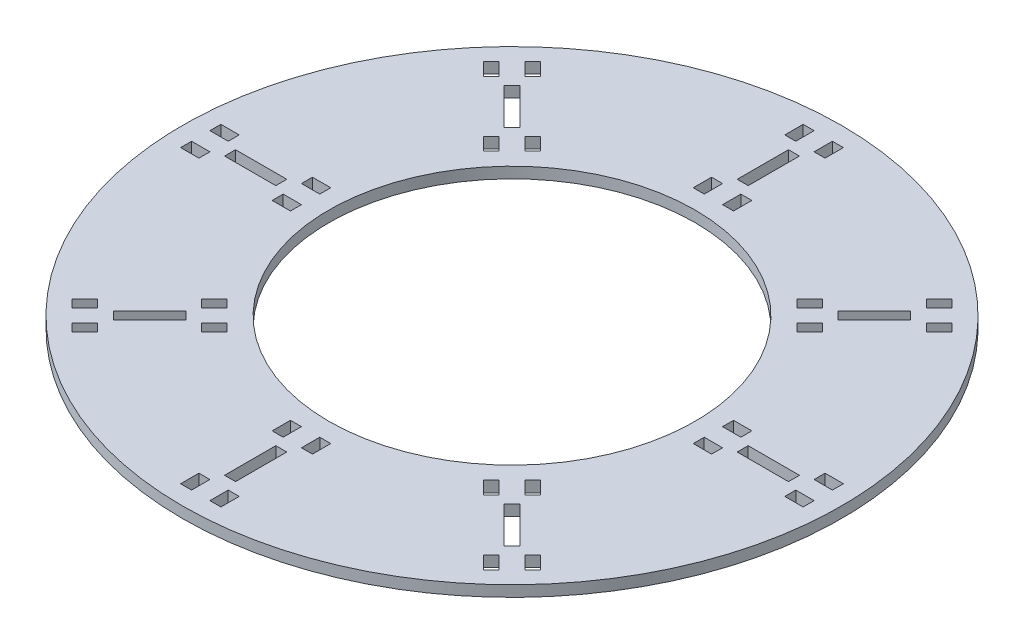
SolidWorks part; units mm, degrees
ref_plane "Front Plane" through (0, 0, 0) normal (0, 0, 1) x (1, 0, 0)
ref_plane "Top Plane" through (0, 0, 0) normal (0, 1, 0) x (1, 0, 0)
ref_plane "Right Plane" through (0, 0, 0) normal (1, 0, 0) x (0, 0, -1)
sketch "Sketch1" plane through (0, 0, 0) normal (0, 1, 0) x (1, 0, 0)
  circle A0 centre (0, 0) radius 90
  dimension "D1" = 180
extrude "Boss-Extrude1" add sketch "Sketch1" along normal blind 3
sketch "Sketch2" plane through (0, 3, 0) normal (0, 1, 0) x (1, 0, 0)
  line L1 (-1.5, 77) -> (1.5, 77)
  line L2 (-1.5, 77) -> (-1.5, 63)
  line L3 (-1.5, 63) -> (1.5, 63)
  line L4 (1.5, 77) -> (1.5, 63)
  point P4 (0, 63)
  point P6 (-1.5, 70)
  dimension "D1" = 3
  dimension "D2" = 14
  dimension "D3" = 70
extrude "Cut-Extrude2" cut sketch "Sketch2" against normal blind 3
sketch "Sketch15" plane through (0, 3, 0) normal (0, 1, 0) x (1, 0, 0)
  line L0 (0, 0) -> (0, 45.806) construction
pattern_circular "CirPattern1" count 8 over 360 about axis through (0, 0, 0) along (0, 1, 0) of "Cut-Extrude2"
sketch "Sketch16" plane through (0, 3, 0) normal (0, 1, 0) x (1, 0, 0)
  line L0 (-1.5, 77) -> (-1.5, 63) construction
  line L1 (-5.5, 85) -> (-2.5, 85)
  line L2 (-5.5, 85) -> (-5.5, 80)
  line L3 (-5.5, 80) -> (-2.5, 80)
  line L4 (-2.5, 85) -> (-2.5, 80)
  line L6 (2.5, 85) -> (5.5, 85)
  line L7 (2.5, 85) -> (2.5, 80)
  line L8 (2.5, 80) -> (5.5, 80)
  line L9 (5.5, 85) -> (5.5, 80)
  line L10 (-5.5, 60) -> (-2.5, 60)
  line L11 (-5.5, 60) -> (-5.5, 55)
  line L12 (-5.5, 55) -> (-2.5, 55)
  line L13 (-2.5, 60) -> (-2.5, 55)
  line L14 (2.5, 60) -> (5.5, 60)
  line L15 (2.5, 60) -> (2.5, 55)
  line L16 (2.5, 55) -> (5.5, 55)
  line L17 (5.5, 60) -> (5.5, 55)
  line L19 (1.5, 63) -> (1.5, 77) construction
  point P21 (1.5, 70)
  point P22 (-1.5, 70)
  dimension "D1" = 5
  dimension "D2" = 3
  dimension "D3" = 1
  dimension "D4" = 3
  dimension "D5" = 5
  dimension "D6" = 10
  dimension "D7" = 10
  dimension "D8" = 5
  dimension "D9" = 10
  dimension "D10" = 1
  dimension "D11" = 4
  dimension "D12" = 3
  dimension "D13" = 10
  dimension "D14" = 5
  dimension "D15" = 3
  dimension "D16" = 1
extrude "Cut-Extrude5" cut sketch "Sketch16" against normal blind 3
pattern_circular "CirPattern2" count 8 over 360 about axis through (0, 0, 0) along (0, 1, 0) of "Cut-Extrude5"
sketch "Sketch24" plane through (0, 3, 0) normal (0, 1, 0) x (1, 0, 0)
  circle A0 centre (0, 0) radius 50
  dimension "D1" = 100
extrude "Cut-Extrude6" cut sketch "Sketch24" against normal blind 3
sketch "Sketch25" plane through (0, 3, 0) normal (0, 1, 0) x (1, 0, 0)
  text T0 "B4" font "Century Gothic" height in points 22
  dimension "D1" = 67.5
  dimension "D2" = 3.5
